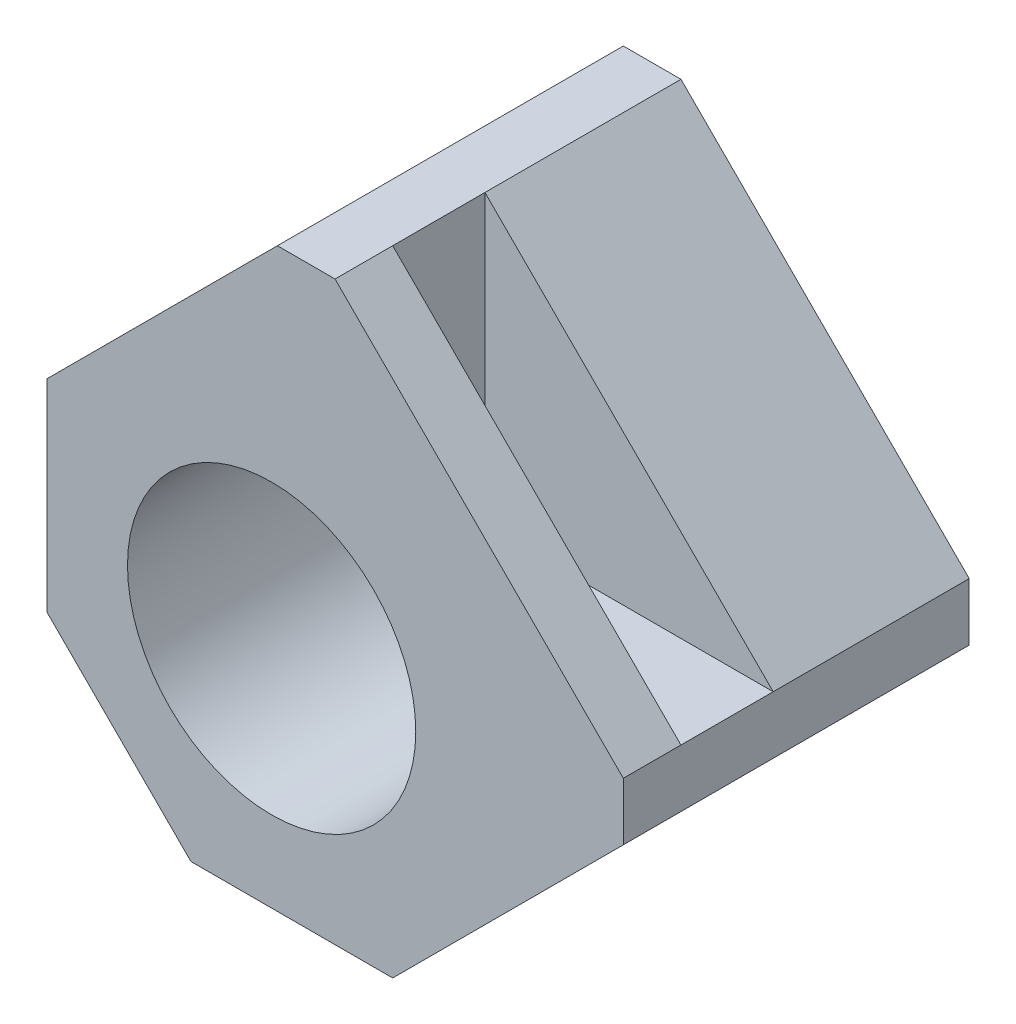
SolidWorks part; units mm, degrees
ref_plane "Plan de face" through (0, 0, 0) normal (0, 0, 1) x (1, 0, 0)
ref_plane "Plan de dessus" through (0, 0, 0) normal (0, 1, 0) x (1, 0, 0)
ref_plane "Plan de droite" through (0, 0, 0) normal (1, 0, 0) x (0, 0, -1)
sketch "Esquisse1" plane through (0, 0, 0) normal (0, 0, 1) x (1, 0, 0)
  line L1 (0, 0) -> (20, 0)
  line L2 (0, 0) -> (0, 20)
  line L3 (0, 20) -> (20, 20)
  line L4 (20, 0) -> (20, 20)
  dimension "D1" = 20
  dimension "D2" = 20
extrude "Boss.-Extru.1" add sketch "Esquisse1" along normal blind 12
chamfer "Chanfrein1" distance 10 angle 45 1 edges at (20, 20, 6)
sketch "Esquisse2" plane through (0, 0, 12) normal (0, 0, 1) x (1, 0, 0)
  line L0 (10, 20) -> (10, 10)
  line L1 (10, 10) -> (20, 10)
  line L2 (20, 10) -> (10, 20)
extrude "Enlèv. mat.-Extru.1" cut sketch "Esquisse2" against normal blind 3.2 from offset 2 offset against normal yes
sketch "Esquisse3" plane through (0, 0, 0) normal (0, 0, -1) x (-1, 0, 0)
  line L0 (-10, 0) -> (-10, 20) construction
  line L1 (0, 0) -> (-20, 0) construction
  line L2 (-20, 10) -> (0, 10) construction
  line L3 (0, 20) -> (0, 0) construction
  circle A0 centre (-7.8, 7.8) radius 2.2
  dimension "D1" = 4.4
extrude "Enlèv. mat.-Extru.2" cut sketch "Esquisse3" against normal through all
sketch "Esquisse4" plane through (0, 0, 12) normal (0, 0, 1) x (1, 0, 0)
  circle A0 centre (7.8, 7.8) radius 5
  dimension "D1" = 10
extrude "Enlèv. mat.-Extru.3" cut sketch "Esquisse4" against normal blind 10.5
chamfer "Chanfrein2" distance 5 angle 45 1 edges at (0, 0, 6)
chamfer "Chanfrein3" distance 8 angle 45 2 edges at (20, 0, 6) (0, 20, 6)
sketch "Sketch1" plane through (0, 0, 0) normal (0, 0, -1) x (-1, 0, 0)
  circle A0 centre (-7.8, 7.8) radius 6
  dimension "D1" = 12
extrude "Cut-Extrude1" cut sketch "Sketch1" against normal blind 0.5
